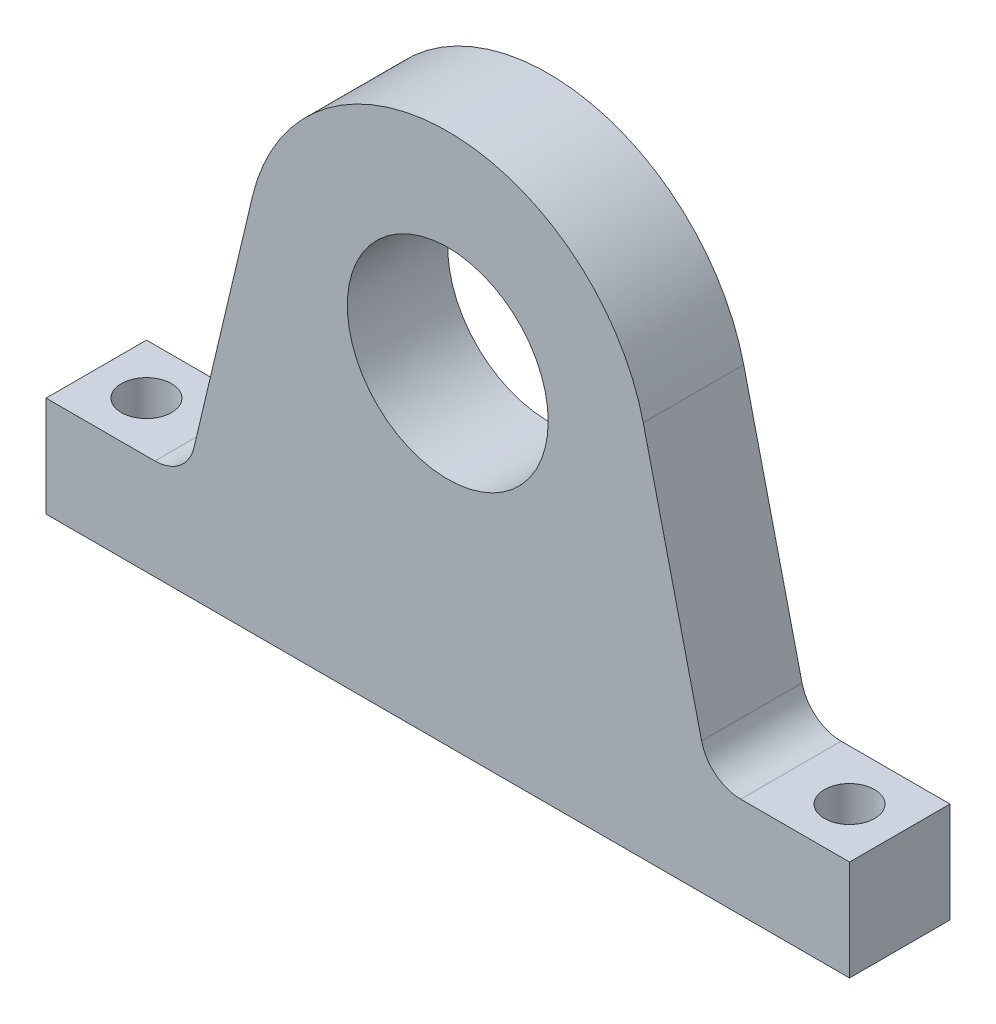
SolidWorks part; units mm, degrees
ref_plane "Front Plane" through (0, 0, 0) normal (0, 0, 1) x (1, 0, 0)
ref_plane "Top Plane" through (0, 0, 0) normal (0, 1, 0) x (1, 0, 0)
ref_plane "Right Plane" through (0, 0, 0) normal (1, 0, 0) x (0, 0, -1)
sketch "Sketch1" plane through (0, 0, 0) normal (0, 0, 1) x (1, 0, 0)
  line L0 (0, -1000) -> (0, 49000) construction
  line L1 (50.8, -41.91) -> (-50.8, -41.91)
  line L2 (50.8, -41.91) -> (50.8, -29.21)
  line L7 (50.8, -29.21) -> (33.02, -29.21)
  line L8 (-50.8, -41.91) -> (-50.8, -29.21)
  line L9 (50.8, -41.91) -> (-50.8, -29.21) construction
  line L10 (50.8, -29.21) -> (-50.8, -41.91) construction
  line L11 (-33.02, -29.21) -> (-33.02, -41.91) construction
  line L12 (33.02, -29.21) -> (33.02, -41.91) construction
  line L13 (-1000, 0) -> (49000, 0) construction
  line L14 (-33.02, -29.21) -> (-24.7164, 5.8533)
  line L16 (33.02, -29.21) -> (24.7164, 5.8533)
  line L17 (-24.7164, 5.8533) -> (-12.683, 56.666) construction
  line L18 (24.7164, 5.8533) -> (12.2424, 58.5265) construction
  line L19 (0, -29.21) -> (-33.02, -29.21) construction
  line L20 (-33.02, -29.21) -> (-50.8, -29.21)
  line L21 (33.02, -29.21) -> (0, -29.21) construction
  circle A2 centre (0, 0) radius 12.7
  arc A3 (24.7164, 5.8533) -> (-24.7164, 5.8533) centre (0, 0) ccw
  arc A4 (0, -25.4) -> (25.4, 0) centre (0, 0) ccw construction
  arc A5 (-25.4, 0) -> (0, -25.4) centre (0, 0) ccw construction
  arc A6 (-24.7164, 5.8533) -> (-25.4, 0) centre (0, 0) ccw construction
  arc A7 (25.4, 0) -> (24.7164, 5.8533) centre (0, 0) ccw construction
  point P3 (0, -35.56)
  point P8 (0, -25.4)
  dimension "D1" = 50.8
  dimension "D2" = 25.4
  dimension "D5" = 3.81
  dimension "D4" = 101.6
  dimension "D3" = 12.7
  dimension "D6" = 17.78
  dimension "D7" = 17.78
extrude "Boss-Extrude1" add sketch "Sketch1" along normal blind 12.7
sketch "Sketch2" plane through (0, -29.21, 0) normal (0, 1, 0) x (1, 0, 0)
  line L2 (-3050.8, -6.35) -> (46949.2, -6.35) construction
  line L3 (-50.8, -12.7) -> (-50.8, 0) construction
  line L4 (50.8, -12.7) -> (50.8, 0) construction
  circle A0 centre (-44.45, -6.35) radius 3.175
  circle A1 centre (44.45, -6.35) radius 3.175
  point P10 (-50.8, -6.35)
  point P11 (21949.2, -6.35)
  dimension "D3" = 6.35
  dimension "D4" = 6.35
  dimension "D1" = 6.35
  dimension "D2" = 6.35
extrude "Cut-Extrude1" cut sketch "Sketch2" against normal through all
fillet "Fillet1" radius 5.08 2 edges at (33.02, -29.21, 6.35) (-33.02, -29.21, 6.35)
